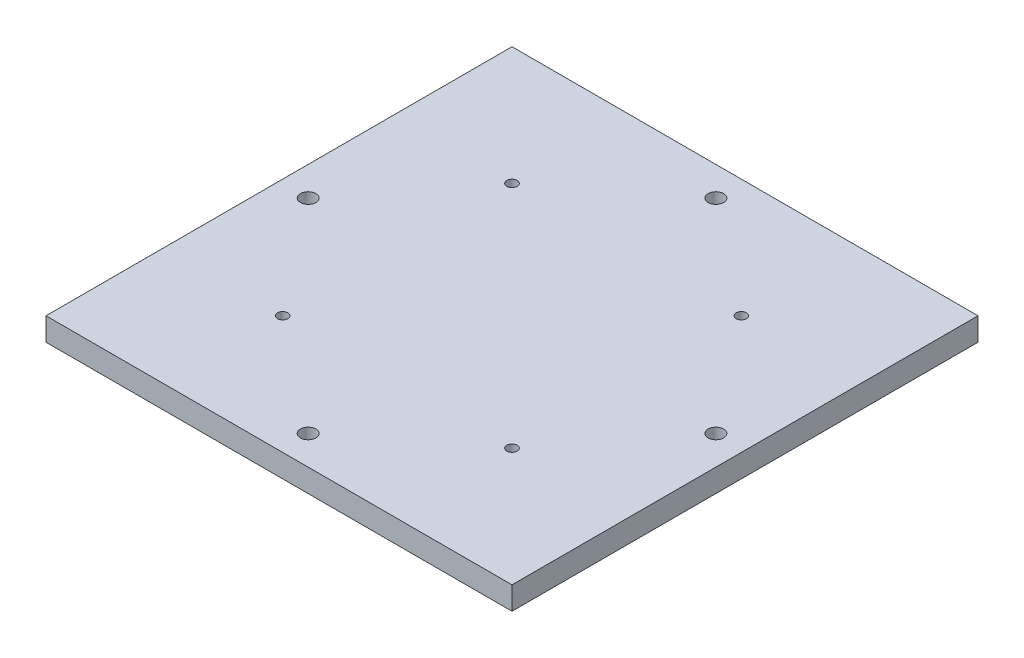
SolidWorks part; units mm, degrees
ref_plane "Front Plane" through (0, 0, 0) normal (0, 0, 1) x (1, 0, 0)
ref_plane "Top Plane" through (0, 0, 0) normal (0, 1, 0) x (1, 0, 0)
ref_plane "Right Plane" through (0, 0, 0) normal (1, 0, 0) x (0, 0, -1)
sketch "Sketch1" plane through (0, 0, 0) normal (0, 1, 0) x (1, 0, 0)
  line L0 (44.1, 44.1) -> (159.1, 44.1)
  line L1 (0, 0) -> (203.2, 0)
  line L2 (0, 0) -> (0, 203.2)
  line L3 (0, 203.2) -> (203.2, 203.2)
  line L4 (203.2, 0) -> (203.2, 203.2)
  line L5 (44.1, 44.1) -> (44.1, 159.1)
  line L6 (44.1, 159.1) -> (159.1, 159.1)
  line L7 (159.1, 44.1) -> (159.1, 159.1)
  circle A0 centre (51.6, 51.6) radius 2.25
  circle A1 centre (151.6, 51.6) radius 2.25
  circle A2 centre (151.6, 151.6) radius 2.25
  circle A3 centre (51.6, 151.6) radius 2.25
  dimension "D6" = 4.5
  dimension "D1" = 203.2
  dimension "D2" = 203.2
  dimension "D3" = 115
  dimension "D4" = 115
  dimension "D9" = 100
  dimension "D10" = 100
  dimension "D11" = 100
  dimension "D12" = 7.5
  dimension "D13" = 7.5
  dimension "D14" = 44.1
  dimension "D15" = 44.1
extrude "Boss-Extrude1" add sketch "Sketch1" along normal blind 10 contours L1 L4 L3 L2 L7 L0 L5 L6 | L0 L7 L6 L5 A3 A2 A1 A0
sketch "Sketch4" plane through (0, 10, 0) normal (0, 1, 0) x (1, 0, 0)
  line L0 (0, 0) -> (0, 203.2) construction
  line L1 (0, 203.2) -> (203.2, 203.2) construction
  circle A0 centre (12.7, 101.6) radius 3.38
  circle A1 centre (190.5, 101.6) radius 3.38
  circle A2 centre (101.6, 190.5) radius 3.38
  circle A3 centre (101.6, 12.7) radius 3.38
  dimension "D1" = 6.76
  dimension "D2" = 177.8
  dimension "D3" = 177.8
  dimension "D4" = 12.7
  dimension "D5" = 12.7
  dimension "D6" = 101.6
  dimension "D7" = 101.6
extrude "Cut-Extrude1" cut sketch "Sketch4" against normal through all contours A3 | A0 | A2 | A1
